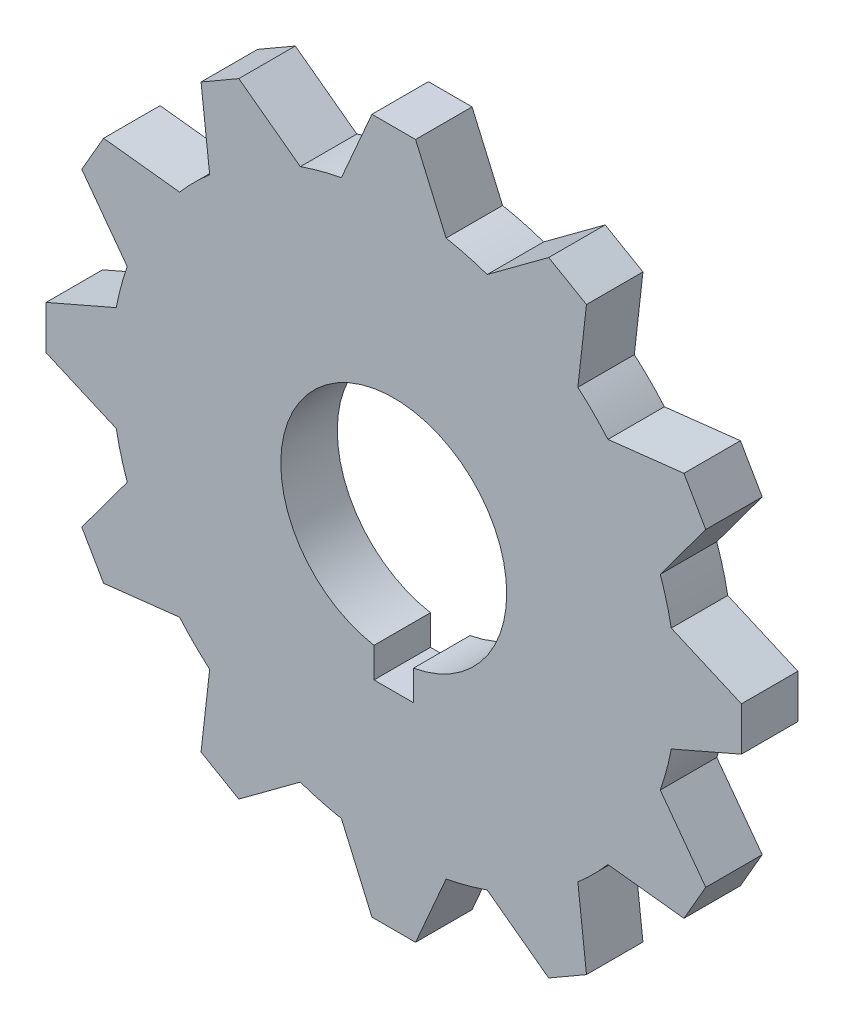
SolidWorks part; units mm, degrees
ref_plane "Front Plane" through (0, 0, 0) normal (0, 0, 1) x (1, 0, 0)
ref_plane "Top Plane" through (0, 0, 0) normal (0, 1, 0) x (1, 0, 0)
ref_plane "Right Plane" through (0, 0, 0) normal (1, 0, 0) x (0, 0, -1)
sketch "Sketch1" plane through (0, 0, 0) normal (0, 0, 1) x (1, 0, 0)
  line L1 (-3.8621, 61.5514) -> (3.8621, 61.5514)
  line L2 (3.8621, 61.5514) -> (9.2675, 49.1336)
  line L3 (-3.8621, 61.5514) -> (-9.2675, 49.1336)
  line L4 (27.4311, 55.2361) -> (16.5409, 47.1847)
  line L5 (27.4311, 55.2361) -> (34.1204, 51.3741)
  line L6 (34.1204, 51.3741) -> (32.5927, 37.9172)
  line L7 (51.3741, 34.1204) -> (37.9172, 32.5927)
  line L8 (51.3741, 34.1204) -> (55.2361, 27.4311)
  line L9 (55.2361, 27.4311) -> (47.1847, 16.5409)
  line L10 (61.5514, 3.8621) -> (49.1336, 9.2675)
  line L11 (61.5514, 3.8621) -> (61.5514, -3.8621)
  line L12 (61.5514, -3.8621) -> (49.1336, -9.2675)
  line L13 (55.2361, -27.4311) -> (47.1847, -16.5409)
  line L14 (55.2361, -27.4311) -> (51.3741, -34.1204)
  line L15 (51.3741, -34.1204) -> (37.9172, -32.5927)
  line L16 (34.1204, -51.3741) -> (32.5927, -37.9172)
  line L17 (34.1204, -51.3741) -> (27.4311, -55.2361)
  line L18 (27.4311, -55.2361) -> (16.5409, -47.1847)
  line L19 (3.8621, -61.5514) -> (9.2675, -49.1336)
  line L20 (3.8621, -61.5514) -> (-3.8621, -61.5514)
  line L21 (-3.8621, -61.5514) -> (-9.2675, -49.1336)
  line L22 (-27.4311, -55.2361) -> (-16.5409, -47.1847)
  line L23 (-27.4311, -55.2361) -> (-34.1204, -51.3741)
  line L24 (-34.1204, -51.3741) -> (-32.5927, -37.9172)
  line L25 (-51.3741, -34.1204) -> (-37.9172, -32.5927)
  line L26 (-51.3741, -34.1204) -> (-55.2361, -27.4311)
  line L27 (-55.2361, -27.4311) -> (-47.1847, -16.5409)
  line L28 (-61.5514, -3.8621) -> (-49.1336, -9.2675)
  line L29 (-61.5514, -3.8621) -> (-61.5514, 3.8621)
  line L30 (-61.5514, 3.8621) -> (-49.1336, 9.2675)
  line L31 (-55.2361, 27.4311) -> (-47.1847, 16.5409)
  line L32 (-55.2361, 27.4311) -> (-51.3741, 34.1204)
  line L33 (-51.3741, 34.1204) -> (-37.9172, 32.5927)
  line L34 (-34.1204, 51.3741) -> (-32.5927, 37.9172)
  line L35 (-34.1204, 51.3741) -> (-27.4311, 55.2361)
  line L36 (-27.4311, 55.2361) -> (-16.5409, 47.1847)
  arc A0 (-49.1336, -9.2675) -> (-47.1847, -16.5409) centre (0, 0) ccw
  arc A1 (-47.1847, 16.5409) -> (-49.1336, 9.2675) centre (0, 0) ccw
  arc A2 (-32.5927, 37.9172) -> (-37.9172, 32.5927) centre (0, 0) ccw
  arc A3 (-9.2675, 49.1336) -> (-16.5409, 47.1847) centre (0, 0) ccw
  arc A4 (16.5409, 47.1847) -> (9.2675, 49.1336) centre (0, 0) ccw
  arc A5 (37.9172, 32.5927) -> (32.5927, 37.9172) centre (0, 0) ccw
  arc A6 (49.1336, 9.2675) -> (47.1847, 16.5409) centre (0, 0) ccw
  arc A7 (47.1847, -16.5409) -> (49.1336, -9.2675) centre (0, 0) ccw
  arc A8 (32.5927, -37.9172) -> (37.9172, -32.5927) centre (0, 0) ccw
  arc A9 (9.2675, -49.1336) -> (16.5409, -47.1847) centre (0, 0) ccw
  arc A10 (-16.5409, -47.1847) -> (-9.2675, -49.1336) centre (0, 0) ccw
  arc A11 (-37.9172, -32.5927) -> (-32.5927, -37.9172) centre (0, 0) ccw
  point P9 (0, 61.5514)
  point P55 (0, 0)
  dimension "D1" = 12
extrude "Boss-Extrude1" add sketch "Sketch1" along normal blind 10 contours L28 A0 L27 L26 L25 A11 L24 L23 L22 A10 L21 L20 L19 A9 L18 L17 L16 A8 L15 L14 L13 A7 L12 L11 L10 A6 L9 L8 L7 A5 L6 L5 L4 A4 L2 L1 L3 A3 L36 L35 L34 A2 L33 L32 L31 A1 L30 L29
sketch "Sketch2" plane through (0, 0, 0) normal (0, 0, -1) x (-1, 0, 0)
  line L1 (0, -25) -> (-3.5, -25)
  line L2 (0, -25) -> (3.5, -25)
  line L3 (3.5, -25) -> (3.5, -19.6914)
  line L4 (-3.5, -25) -> (-3.5, -19.6914)
  arc A0 (3.5, -19.6914) -> (-3.5, -19.6914) centre (0, 0) ccw
extrude "Cut-Extrude1" cut sketch "Sketch2" against normal blind 10 contours L3 A0 L4 L1 L2
